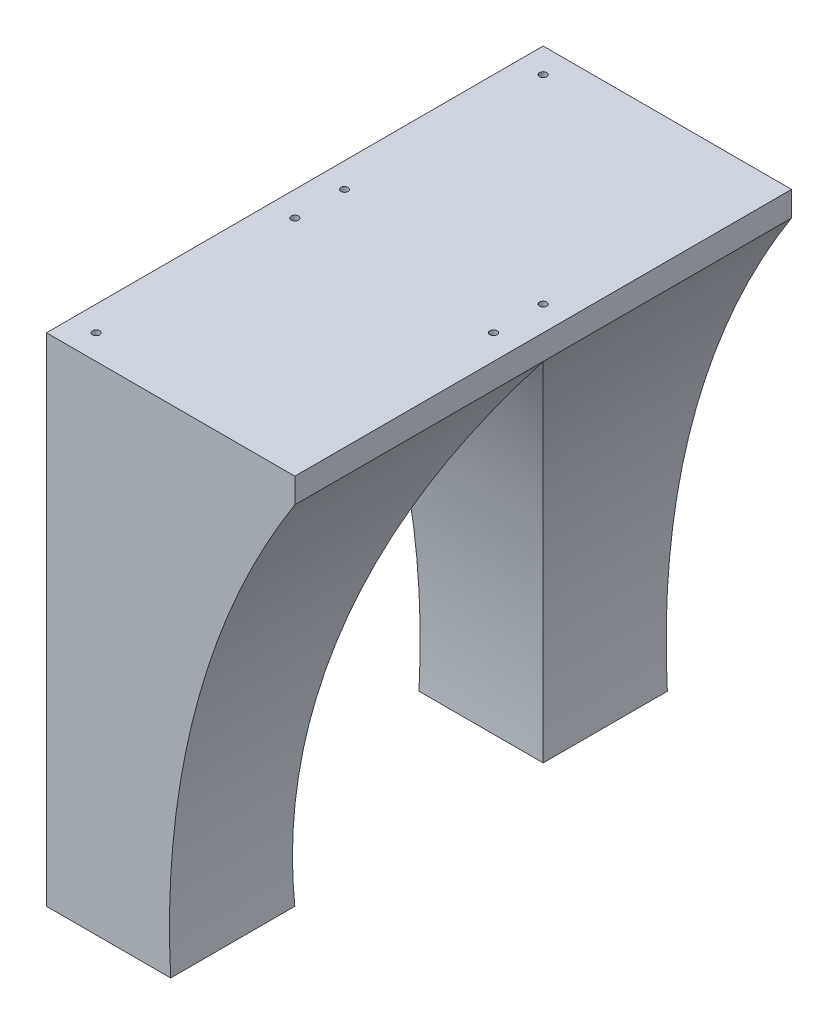
SolidWorks part; units mm, degrees
material "ABS"
ref_plane "Front Plane" through (0, 0, 0) normal (0, 0, 1) x (1, 0, 0)
ref_plane "Top Plane" through (0, 0, 0) normal (0, 1, 0) x (1, 0, 0)
ref_plane "Right Plane" through (0, 0, 0) normal (1, 0, 0) x (0, 0, -1)
sketch "Sketch1" plane through (0, 0, 0) normal (0, 1, 0) x (1, 0, 0)
  line L1 (0, 0) -> (100, 0)
  line L2 (0, 0) -> (0, 100)
  line L3 (0, 100) -> (100, 100)
  line L4 (100, 0) -> (100, 100)
  line L5 (50, 100) -> (50, 0) construction
  line L6 (0, 50) -> (100, 50) construction
  point P152 (50, 50)
  dimension "D1" = 100
  dimension "D2" = 100
extrude "Boss-Extrude1" add sketch "Sketch1" against normal blind 200
sketch "Sketch2" plane through (0, 0, 0) normal (0, 0, 1) x (1, 0, 0)
  line L0 (0, -200) -> (50, -200)
  line L1 (0, -200) -> (100, -200) construction
  line L2 (100, 0) -> (100, -10)
  line L3 (100, -200) -> (100, 0) construction
  line L4 (0, -200) -> (0, 0)
  line L5 (0, 0) -> (100, 0)
  line L6 (50, -200) -> (100, -200)
  line L7 (100, -200) -> (100, -10)
  arc A0 (50, -200) -> (100, -10) centre (369.5214, -182.5056) cw
  line M5 (0, -200) -> (100, -200)
  line M6 (100, -200) -> (100, 0)
  dimension "D3" = 320
  dimension "D1" = 50
  dimension "D2" = 10
extrude "Cut-Extrude1" cut sketch "Sketch2" against normal blind 200 contours A0 M5 M6
sketch "Sketch3" plane through (0, 0, 0) normal (-1, 0, 0) x (0, 0, 1)
  line L0 (0, -200) -> (-50, -200)
  line L1 (-100, -200) -> (0, -200) construction
  line L2 (-100, 0) -> (-100, -10)
  line L3 (-100, -200) -> (-100, 0) construction
  line L4 (-100, -10) -> (-100, -200)
  line L5 (-100, -200) -> (-50, -200)
  arc A0 (-100, -10) -> (-50, -200) centre (-369.5214, -182.5056) cw
  line M4 (-100, 0) -> (-100, -200)
  line M5 (-100, -200) -> (0, -200)
  dimension "D3" = 320
  dimension "D1" = 10
  dimension "D2" = 50
extrude "Cut-Extrude2" cut sketch "Sketch3" against normal blind 200 contours A0 M4 M5
sketch "Sketch4" plane through (0, 0, 0) normal (0, 1, 0) x (1, 0, 0)
  line L5 (100, 0) -> (100, 100) construction
  line L6 (10, 10) -> (90, 10) construction
  line L7 (10, 10) -> (10, 90) construction
  line L8 (10, 90) -> (90, 90) construction
  line L9 (90, 10) -> (90, 90) construction
  line L10 (10, 10) -> (90, 90) construction
  line L11 (10, 90) -> (90, 10) construction
  line L12 (100, 100) -> (0, 100) construction
  circle A0 centre (10, 90) radius 1.45
  circle A1 centre (90, 90) radius 1.45
  circle A3 centre (10, 10) radius 1.45
  point P0 (50, 50)
  point P7 (100, 50)
  point P10 (50, 100)
  dimension "D2" = 2.9
  dimension "D1" = 80
extrude "Cut-Extrude3" cut sketch "Sketch4" against normal blind 10
mirror "Mirror1" about plane through (0, -200, -100) normal (0, 0, -1) of bodies 104
